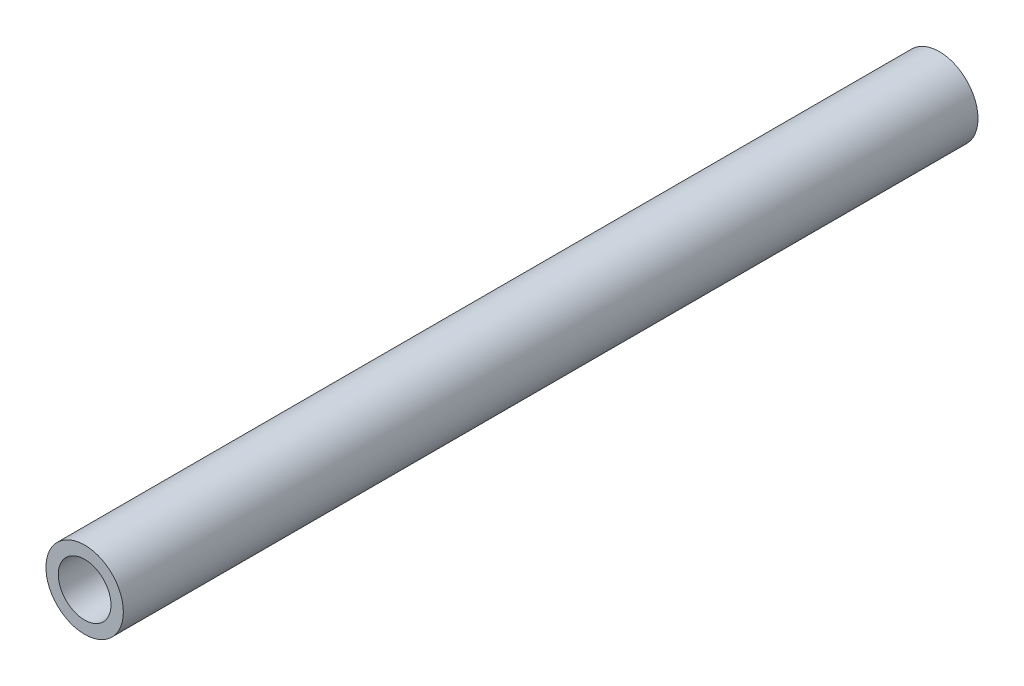
SolidWorks part; units mm, degrees
ref_plane "Front Plane" through (0, 0, 0) normal (0, 0, 1) x (1, 0, 0)
ref_plane "Top Plane" through (0, 0, 0) normal (0, 1, 0) x (1, 0, 0)
ref_plane "Right Plane" through (0, 0, 0) normal (1, 0, 0) x (0, 0, -1)
sketch "Sketch2" plane through (0, 0, 0) normal (0, 0, 1) x (1, 0, 0)
  circle A0 centre (-36.481, 23.3453) radius 4.25
  circle A1 centre (-36.481, 23.3453) radius 6.25
extrude "Boss-Extrude1" add sketch "Sketch2" along normal blind 138
